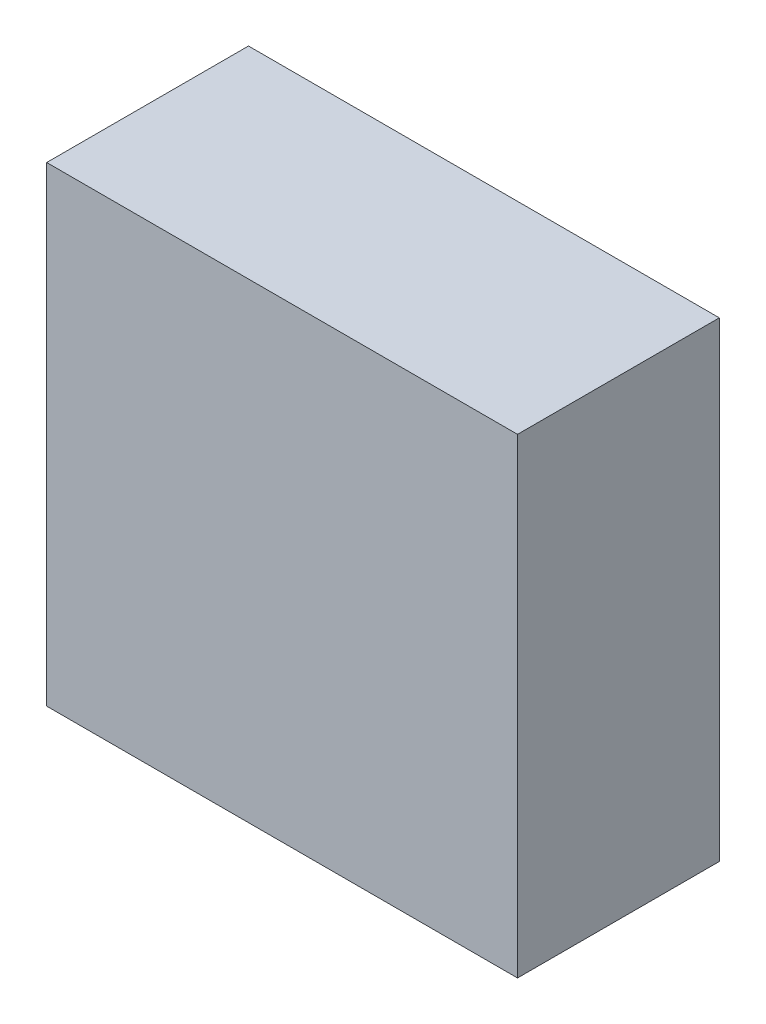
SolidWorks part; units mm, degrees
ref_plane "Front Plane" through (0, 0, 0) normal (0, 0, 1) x (1, 0, 0)
ref_plane "Top Plane" through (0, 0, 0) normal (0, 1, 0) x (1, 0, 0)
ref_plane "Right Plane" through (0, 0, 0) normal (1, 0, 0) x (0, 0, -1)
sketch "Sketch1" plane through (0, 0, 0) normal (0, 0, 1) x (1, 0, 0)
  line L1 (-7, 7) -> (7, 7)
  line L2 (-7, 7) -> (-7, -7)
  line L3 (-7, -7) -> (7, -7)
  line L4 (7, 7) -> (7, -7)
  line L5 (-7, 7) -> (7, -7) construction
  line L6 (-7, -7) -> (7, 7) construction
  point P0 (0, 0)
  dimension "D1" = 14
  dimension "D2" = 14
extrude "Boss-Extrude1" add sketch "Sketch1" along normal blind 6
